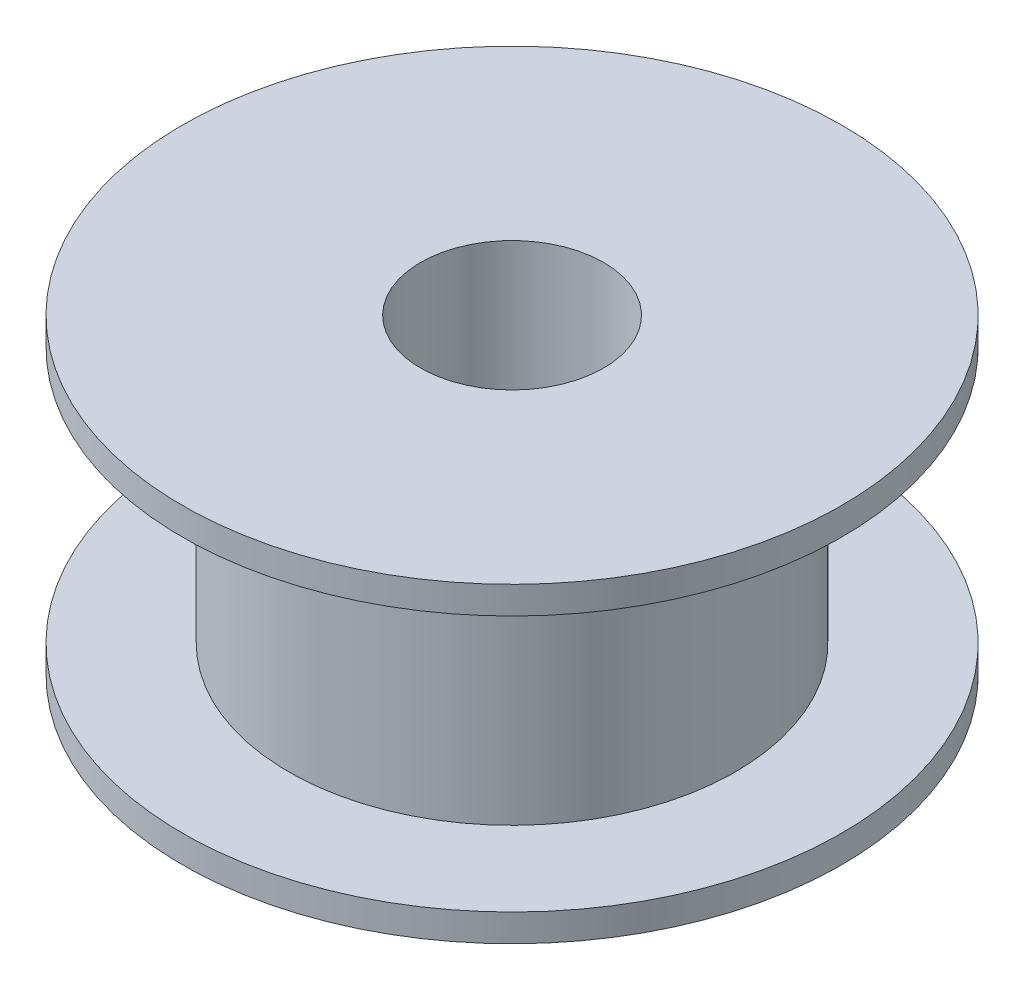
SolidWorks part; units mm, degrees
ref_plane "Front" through (0, 0, 0) normal (0, 0, 1) x (1, 0, 0)
ref_plane "Top" through (0, 0, 0) normal (0, 1, 0) x (1, 0, 0)
ref_plane "Right" through (0, 0, 0) normal (1, 0, 0) x (0, 0, -1)
sketch "Sketch1" plane through (0, 0, 0) normal (0, 0, 1) x (1, 0, 0)
  line L0 (0, 0) -> (0, 8.5) construction
  line L1 (2.5, 0) -> (2.5, 8.5)
  line L2 (2.5, 8.5) -> (9, 8.5)
  line L3 (9, 8.5) -> (9, 7.75)
  line L4 (9, 7.75) -> (6.1, 7.75)
  line L5 (6.1, 7.75) -> (6.1, 0.75)
  line L6 (6.1, 0.75) -> (9, 0.75)
  line L7 (9, 0.75) -> (9, 0)
  line L8 (9, 0) -> (2.5, 0)
  dimension "D1" = 8.5
  dimension "D2" = 7
  dimension "D3" = 18
  dimension "D4" = 12.2
  dimension "D5" = 2.5
revolve "Revolve1" add sketch "Sketch1" angle 360 about L0
